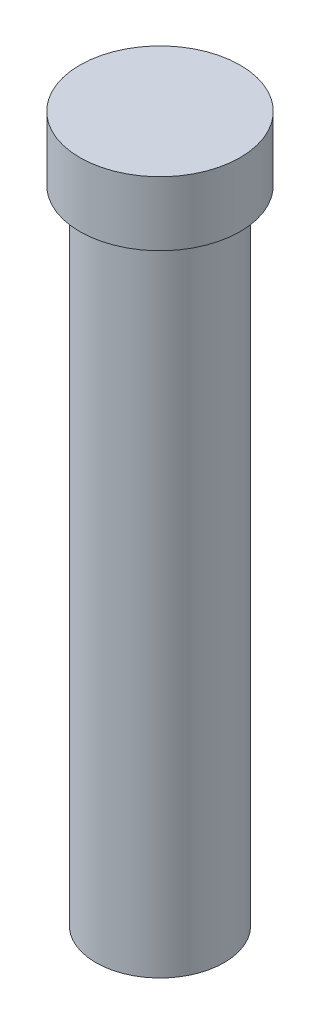
SolidWorks part; units mm, degrees
ref_plane "Front Plane" through (0, 0, 0) normal (0, 0, 1) x (1, 0, 0)
ref_plane "Top Plane" through (0, 0, 0) normal (0, 1, 0) x (1, 0, 0)
ref_plane "Right Plane" through (0, 0, 0) normal (1, 0, 0) x (0, 0, -1)
sketch "Sketch1" plane through (0, 0, 0) normal (0, 1, 0) x (1, 0, 0)
  circle A0 centre (0, 0) radius 2
  dimension "D1" = 4
extrude "Boss-Extrude1" add sketch "Sketch1" along normal blind 20
sketch "Sketch2" plane through (0, 20, 0) normal (0, 1, 0) x (1, 0, 0)
  circle A0 centre (0, 0) radius 2.5
  dimension "D1" = 5
extrude "Boss-Extrude2" add sketch "Sketch2" along normal blind 2
